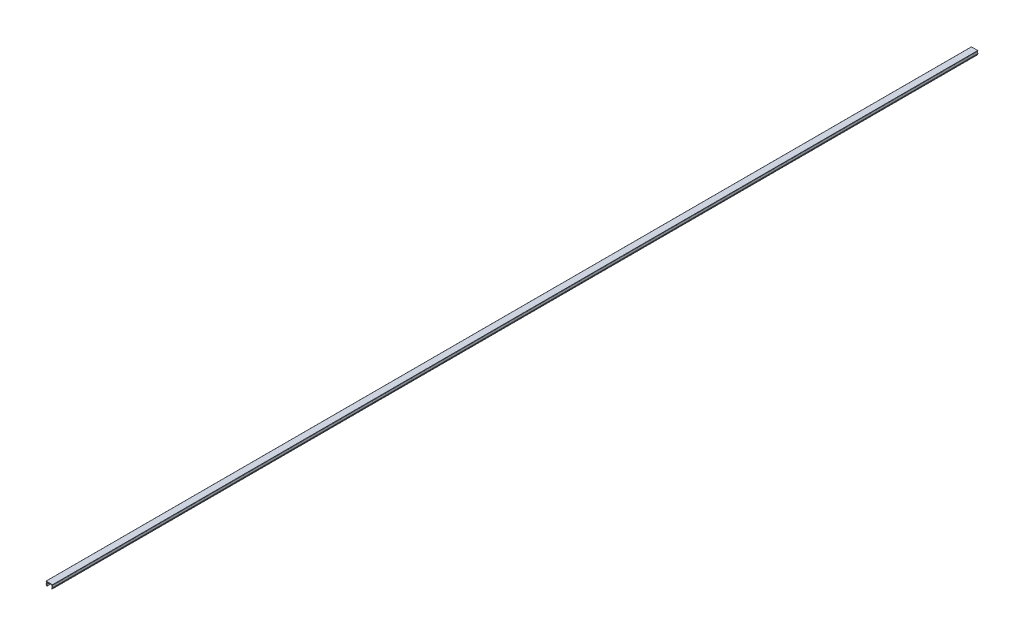
SolidWorks part; units mm, degrees
ref_plane "前视基准面" through (0, 0, 0) normal (0, 0, 1) x (1, 0, 0)
ref_plane "上视基准面" through (0, 0, 0) normal (0, 1, 0) x (1, 0, 0)
ref_plane "右视基准面" through (0, 0, 0) normal (1, 0, 0) x (0, 0, -1)
sketch "草图1" plane through (0, 0, 0) normal (0, 0, 1) x (1, 0, 0)
  line L1 (3.7198, 85.7782) -> (3.2779, 86.9923)
  line L2 (3.749, 87.093) -> (4.1682, 85.9414)
  line L3 (4.1807, 89.6182) -> (3.7445, 87.1446)
  line L4 (9.1652, 89.6182) -> (4.1807, 89.6182)
  line L5 (9.6014, 87.1446) -> (9.1652, 89.6182)
  line L6 (9.1777, 85.9414) -> (9.5969, 87.093)
  line L7 (10.0679, 86.9923) -> (9.626, 85.7782)
  line L8 (9.6729, 89.6182) -> (10.0905, 87.2502)
  line L9 (10.1729, 89.6182) -> (9.6729, 89.6182)
  line L10 (10.2729, 89.9182) -> (10.2729, 89.7182)
  line L11 (3.2729, 90.1182) -> (10.0729, 90.1182)
  line L12 (3.0729, 89.7182) -> (3.0729, 89.9182)
  line L13 (3.6729, 89.6182) -> (3.1729, 89.6182)
  line L14 (3.2554, 87.2502) -> (3.6729, 89.6182)
  arc A0 (3.2554, 87.2502) -> (3.2779, 86.9923) centre (3.7478, 87.1633) ccw
  arc A1 (3.7198, 85.7782) -> (4.1682, 85.9414) centre (3.944, 85.8598) ccw
  arc A2 (3.7445, 87.1446) -> (3.749, 87.093) centre (3.843, 87.1272) ccw
  arc A3 (9.5969, 87.093) -> (9.6014, 87.1446) centre (9.5029, 87.1272) ccw
  arc A4 (9.1777, 85.9414) -> (9.626, 85.7782) centre (9.4019, 85.8598) ccw
  arc A5 (10.0679, 86.9923) -> (10.0905, 87.2502) centre (9.5981, 87.1633) ccw
  arc A6 (10.1729, 89.6182) -> (10.2729, 89.7182) centre (10.1729, 89.7182) ccw
  arc A7 (10.2729, 89.9182) -> (10.0729, 90.1182) centre (10.0729, 89.9182) ccw
  arc A8 (3.2729, 90.1182) -> (3.0729, 89.9182) centre (3.2729, 89.9182) ccw
  arc A9 (3.0729, 89.7182) -> (3.1729, 89.6182) centre (3.1729, 89.7182) ccw
extrude "拉伸1" add sketch "草图1" along normal blind 1000
